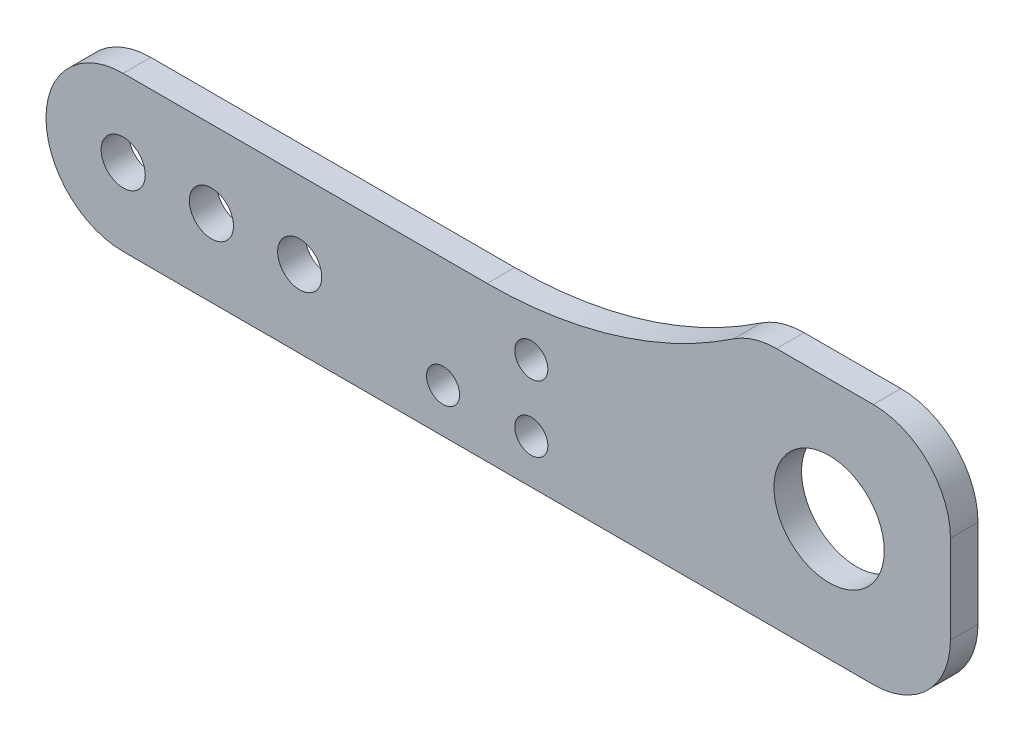
SolidWorks part; units mm, degrees
ref_plane "Front Plane" through (0, 0, 0) normal (0, 0, 1) x (1, 0, 0)
ref_plane "Top Plane" through (0, 0, 0) normal (0, 1, 0) x (1, 0, 0)
ref_plane "Right Plane" through (0, 0, 0) normal (1, 0, 0) x (0, 0, -1)
sketch "Sketch1" plane through (0, 0, 0) normal (0, 0, 1) x (1, 0, 0)
  line L0 (0, 7) -> (33, 7)
  line L1 (68, -7) -> (0, -7)
  line L5 (59.2298, 15) -> (68, 15)
  line L6 (75, 0) -> (75, 8)
  arc A1 (0, -7) -> (0, 7) centre (0, 0) cw
  arc A2 (33, 7) -> (55.3232, 13.8085) centre (33, 47) ccw
  arc A3 (68, -7) -> (75, 0) centre (68, 0) ccw
  arc A4 (68, 15) -> (75, 8) centre (68, 8) cw
  arc A5 (59.2298, 15) -> (55.3232, 13.8085) centre (59.2298, 8) ccw
  point P3 (75, -7)
  point P15 (75, 15)
  point P18 (57, 15)
  dimension "D2" = 7
  dimension "D4" = 40
  dimension "D1" = 7
  dimension "D3" = 22
  dimension "D5" = 18
  dimension "D6" = 75
extrude "Boss-Extrude1" add sketch "Sketch1" along normal blind 2.5
sketch "Sketch2" plane through (0, 0, 2.5) normal (0, 0, 1) x (1, 0, 0)
  line L0 (-7, 0) -> (-7, -7) construction
  line L6 (0, 0) -> (8, 0) construction
  line L7 (8, 0) -> (16, 0) construction
  line L8 (-7, -7) -> (0, -7) construction
  circle A0 centre (0, 0) radius 2
  circle A2 centre (8, 0) radius 2
  circle A5 centre (16, 0) radius 2
  arc A6 (0, 7) -> (0, -7) centre (0, 0) ccw construction
  dimension "D1" = 4
  dimension "D2" = 8
extrude "Cut-Extrude1" cut sketch "Sketch2" against normal up to surface (2.5 mm away) up to face at (47.7635, 5.6039, 0)
sketch "Sketch3" plane through (0, 0, 2.5) normal (0, 0, 1) x (1, 0, 0)
  line L0 (75, 0) -> (75, 8) construction
  line L2 (64, 4) -> (75, 4) construction
  line L3 (64, 4) -> (64, -7) construction
  line L4 (0, -7) -> (68, -7) construction
  circle A0 centre (64, 4) radius 5
  dimension "D1" = 10
extrude "Cut-Extrude2" cut sketch "Sketch3" against normal up to surface (2.5 mm away) up to face at (2, 0, 0)
hole_wizard "Ø3.0mm Dowel Hole2" positions "Sketch9" profile "Sketch10" hole size "Ø3.0" standard "ANSI Metric" end condition through all
sketch "Sketch9" plane through (0, 0, 2.5) normal (0, 0, 1) x (1, 0, 0)
  line L2 (75, 0) -> (75, 8) construction
  line L3 (0, -7) -> (68, -7) construction
  point P0 (29, -3)
  point P3 (37, -3)
  point P6 (37, 3)
  dimension "D1" = 6
  dimension "D2" = 8
  dimension "D3" = 38
  dimension "D4" = 4
sketch "Sketch10" plane through (29, -3, 2.5) normal (1, 0, 0) x (0, -1, 0)
  line L0 (0, 0) -> (0, 2.5)
  line L1 (0, 2.5) -> (1.5, 2.5)
  line L2 (1.5, 2.5) -> (1.5, 0)
  line L5 (1.5, 0) -> (0, 0)
  line L11 (0, -6.35) -> (0, 107.95) construction
  dimension "Thru Hole Dia." = 3
  dimension "Thru Hole Depth" = 2.5
sketch "Sketch4" plane through (0, 0, 2.5) normal (0, 0, -1) x (-1, 0, 0)
  line L0 (0, -7) -> (-68, -7) construction
  line L1 (-49, -7) -> (-23, -7)
  line L2 (-49, -7) -> (-49, 10.3394)
  line L3 (-49, 10.3394) -> (-23, 10.3394)
  line L4 (-23, -7) -> (-23, 10.3394)
  line L5 (-75, 0) -> (-75, 8) construction
  arc A0 (-55.3232, 13.8085) -> (-33, 7) centre (-33, 47) ccw construction
  dimension "D1" = 26
  dimension "D2" = 26
extrude "Cut-Extrude3" [suppressed] cut sketch "Sketch4" along normal blind 1.6
